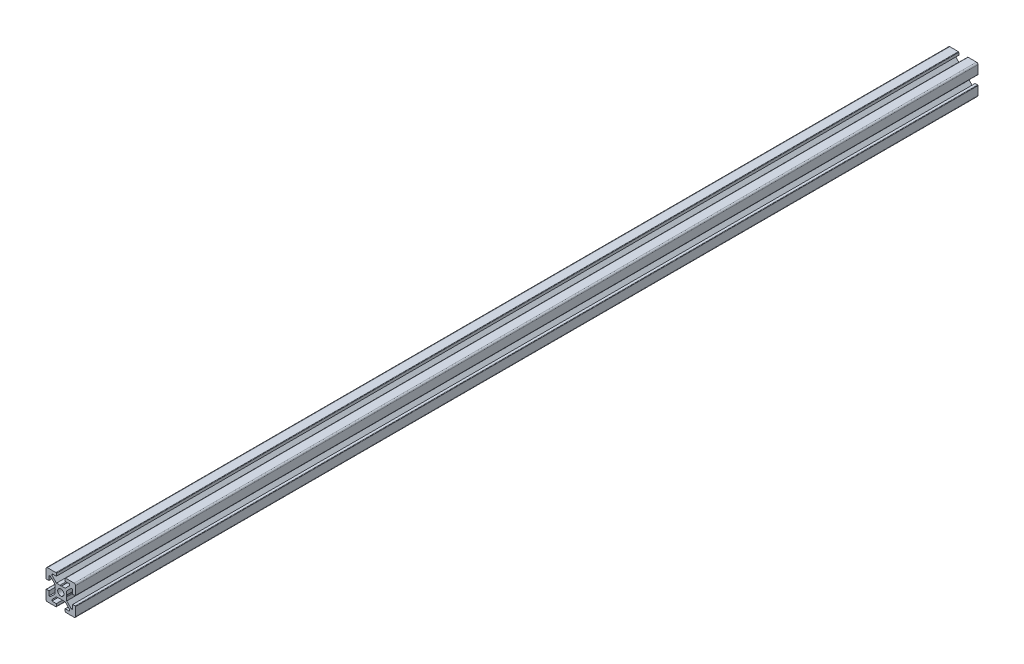
SolidWorks part; units mm, degrees
material "6063-T5"
ref_plane "Front Plane" through (0, 0, 0) normal (0, 0, 1) x (1, 0, 0)
ref_plane "Top Plane" through (0, 0, 0) normal (0, 1, 0) x (1, 0, 0)
ref_plane "Right Plane" through (0, 0, 0) normal (1, 0, 0) x (0, 0, -1)
ref_plane "Plane1" through (0, 0, 0) normal (0, 0, 1) x (1, 0, 0)
sketch "Sketch1" plane through (0, 0, 0) normal (0, 0, 1) x (1, 0, 0)
  line L0 (-10, 9) -> (-10, 3.3)
  line L1 (-9.7, 3) -> (-8, 3)
  line L2 (-8, 3) -> (-8, 6)
  line L3 (-8, 6) -> (-7.0607, 6)
  line L4 (-7.0607, 6) -> (-4, 2.9393)
  line L5 (-4, 2.9393) -> (-4, 0.5196)
  line L6 (-4, 0.5196) -> (-3.7, 0)
  line L7 (-3.7, 0) -> (-4, -0.5196)
  line L8 (-4, -0.5196) -> (-4, -2.9393)
  line L9 (-4, -2.9393) -> (-7.0607, -6)
  line L10 (-7.0607, -6) -> (-8, -6)
  line L11 (-8, -6) -> (-8, -3)
  line L12 (-8, -3) -> (-9.7, -3)
  line L13 (-10, -3.3) -> (-10, -9)
  line L14 (-9, -10) -> (-3.3, -10)
  line L15 (-3, -9.7) -> (-3, -8)
  line L16 (-3, -8) -> (-6, -8)
  line L17 (-6, -8) -> (-6, -7.0607)
  line L18 (-6, -7.0607) -> (-2.9393, -4)
  line L19 (-2.9393, -4) -> (-0.5196, -4)
  line L20 (-0.5196, -4) -> (0, -3.7)
  line L21 (0, -3.7) -> (0.5196, -4)
  line L22 (0.5196, -4) -> (2.9393, -4)
  line L23 (2.9393, -4) -> (6, -7.0607)
  line L24 (6, -7.0607) -> (6, -8)
  line L25 (6, -8) -> (3, -8)
  line L26 (3, -8) -> (3, -9.7)
  line L27 (3.3, -10) -> (9, -10)
  line L28 (10, -9) -> (10, -3.3)
  line L29 (9.7, -3) -> (8, -3)
  line L30 (8, -3) -> (8, -6)
  line L31 (8, -6) -> (7.0606, -6)
  line L32 (7.0606, -6) -> (4, -2.9393)
  line L33 (4, -2.9393) -> (4, -0.5196)
  line L34 (4, -0.5196) -> (3.7, 0)
  line L35 (3.7, 0) -> (4, 0.5196)
  line L36 (4, 0.5196) -> (4, 2.9393)
  line L37 (4, 2.9393) -> (7.0607, 6)
  line L38 (7.0607, 6) -> (8, 6)
  line L39 (8, 6) -> (8, 3)
  line L40 (8, 3) -> (9.7, 3)
  line L41 (10, 3.3) -> (10, 9)
  line L42 (9, 10) -> (3.3, 10)
  line L43 (3, 9.7) -> (3, 8)
  line L44 (3, 8) -> (6, 8)
  line L45 (6, 8) -> (6, 7.0607)
  line L46 (6, 7.0607) -> (2.9393, 4)
  line L47 (2.9393, 4) -> (0.5196, 4)
  line L48 (0.5196, 4) -> (0, 3.7)
  line L49 (0, 3.7) -> (-0.5196, 4)
  line L50 (-0.5196, 4) -> (-2.9394, 4)
  line L51 (-2.9394, 4) -> (-6, 7.0606)
  line L52 (-6, 7.0606) -> (-6, 8)
  line L53 (-6, 8) -> (-3, 8)
  line L54 (-3, 8) -> (-3, 9.7)
  line L55 (-3.3, 10) -> (-9, 10)
  arc A0 (-10, 3.3) -> (-9.7, 3) centre (-9.7, 3.3) ccw
  arc A1 (-9.7, -3) -> (-10, -3.3) centre (-9.7, -3.3) ccw
  arc A2 (-10, -9) -> (-9, -10) centre (-9, -9) ccw
  arc A3 (-3.3, -10) -> (-3, -9.7) centre (-3.3, -9.7) ccw
  arc A4 (3, -9.7) -> (3.3, -10) centre (3.3, -9.7) ccw
  arc A5 (9, -10) -> (10, -9) centre (9, -9) ccw
  arc A6 (10, -3.3) -> (9.7, -3) centre (9.7, -3.3) ccw
  arc A7 (9.7, 3) -> (10, 3.3) centre (9.7, 3.3) ccw
  arc A8 (10, 9) -> (9, 10) centre (9, 9) ccw
  arc A9 (3.3, 10) -> (3, 9.7) centre (3.3, 9.7) ccw
  arc A10 (-3, 9.7) -> (-3.3, 10) centre (-3.3, 9.7) ccw
  arc A11 (-9, 10) -> (-10, 9) centre (-9, 9) ccw
extrude "Boss-Extrude1" add sketch "Sketch1" against normal blind 609.5
ref_plane "Plane2" through (0, 0, 0) normal (1, 0, 0) x (0, 0, -1)
sketch "Sketch2" plane through (0, 0, 0) normal (1, 0, 0) x (0, 0, -1)
  line L0 (0, 0) -> (0, 2.1)
  line L1 (0, 2.1) -> (609.5, 2.1)
  line L2 (609.5, 2.1) -> (609.5, 0)
  line L3 (609.5, 0) -> (0, 0)
  line L4 (609.5, 0) -> (0, 0) construction
revolve "Cut-Revolve1" cut sketch "Sketch2" angle 360 about L4
sketch "Sketch4" plane through (0, 0, 0) normal (0, 1, 0) x (1, 0, 0)
  line L1 (0, 609.5) -> (0, 0) construction
  line L2 (9, 609.5) -> (3.3, 609.5) construction
  line L3 (9, 0) -> (3.3, 0) construction
  circle A0 centre (0, 599.5) radius 2.5
  circle A1 centre (0, 579.5) radius 2.5
  circle A2 centre (0, 559.5) radius 2.5
  circle A3 centre (0, 539.5) radius 2.5
  circle A4 centre (0, 10) radius 2.5
  circle A5 centre (0, 30) radius 2.5
  circle A6 centre (0, 50) radius 2.5
  circle A7 centre (0, 70) radius 2.5
  dimension "D1" = 10
  dimension "D3" = 5
  dimension "D4" = 10
  dimension "D2" = 4
  dimension "D5" = 4
extrude "Cut-Extrude1" cut sketch "Sketch4" against normal blind 10 and the other way blind 10
sketch "Sketch6" plane through (0, 0, 0) normal (1, 0, 0) x (0, 0, -1)
  line L0 (11, 0) -> (-11, 0) construction
  line L1 (0, 11) -> (0, -11) construction
  line L2 (609.5, 3.3) -> (609.5, 9) construction
  circle A0 centre (10, 0) radius 2.5
  circle A1 centre (30, 0) radius 2.5
  circle A2 centre (50, 0) radius 2.5
  circle A3 centre (70, 0) radius 2.5
  circle A4 centre (599.5, 0) radius 2.5
  circle A5 centre (579.5, 0) radius 2.5
  circle A6 centre (559.5, 0) radius 2.5
  circle A7 centre (539.5, 0) radius 2.5
  dimension "D1" = 5
  dimension "D2" = 10
  dimension "D4" = 5
  dimension "D5" = 10
  dimension "D3" = 4
  dimension "D6" = 4
extrude "Cut-Extrude2" cut sketch "Sketch6" against normal blind 10 and the other way blind 10
